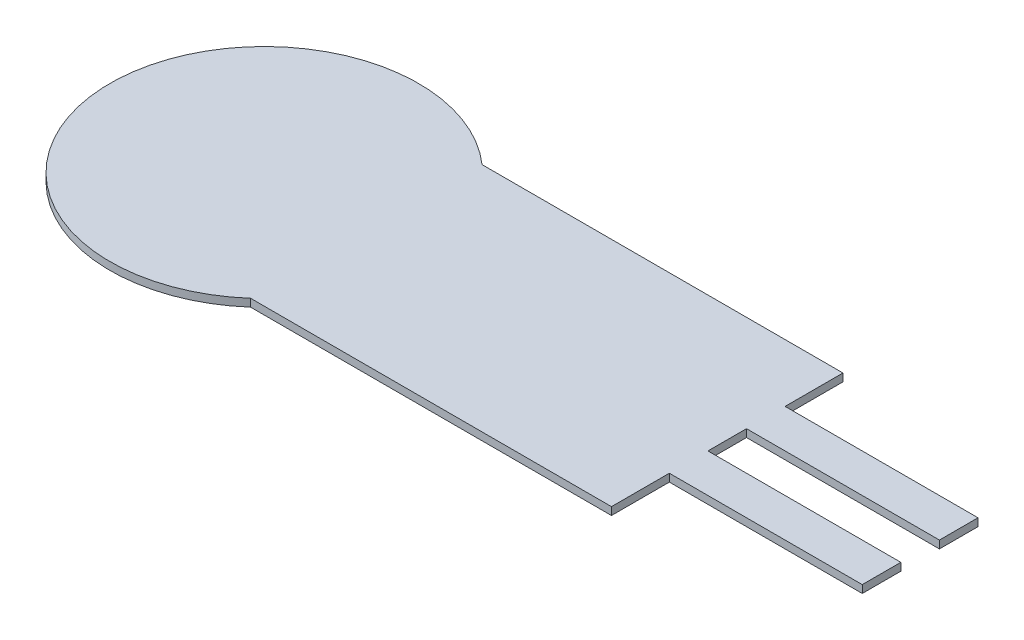
SolidWorks part; units mm, degrees
ref_plane "Front Plane" through (0, 0, 0) normal (0, 0, 1) x (1, 0, 0)
ref_plane "Top Plane" through (0, 0, 0) normal (0, 1, 0) x (1, 0, 0)
ref_plane "Right Plane" through (0, 0, 0) normal (1, 0, 0) x (0, 0, -1)
sketch "Sketch1" plane through (0, 0, 0) normal (0, 1, 0) x (1, 0, 0)
  circle A0 centre (0, 0) radius 4
  dimension "D1" = 8
extrude "Boss-Extrude1" add sketch "Sketch1" along normal mid plane 0.2
sketch "Sketch2" plane through (0, 0, 0) normal (0, 1, 0) x (1, 0, 0)
  line L0 (0, 0) -> (11.5083, 0) construction
  line L1 (0, 3) -> (12, 3)
  line L2 (0, 3) -> (0, -3)
  line L3 (0, -3) -> (12, -3)
  line L4 (12, 3) -> (12, -3)
  circle A0 centre (0, 0) radius 4 construction
  point P10 (-4, 0)
  dimension "D1" = 6
  dimension "D2" = 16
extrude "Boss-Extrude2" add sketch "Sketch2" along normal mid plane 0.2
sketch "Sketch3" plane through (0, 0, 0) normal (0, 1, 0) x (1, 0, 0)
  line L0 (0, 0) -> (17.1919, 0) construction
  line L1 (12, -3) -> (12, 3) construction
  line L2 (12, 1.5) -> (17, 1.5)
  line L3 (12, 1.5) -> (12, 0.5)
  line L4 (12, 0.5) -> (17, 0.5)
  line L5 (17, 1.5) -> (17, 0.5)
  arc A0 (2.6458, 3) -> (2.6458, -3) centre (0, 0) ccw construction
  point P9 (-4, 0)
  dimension "D1" = 3
  dimension "D2" = 1
  dimension "D3" = 21
extrude "Boss-Extrude3" add sketch "Sketch3" along normal mid plane 0.2
mirror "Mirror1" about plane through (0, 0, 0) normal (0, 0, 1) of "Boss-Extrude3"
